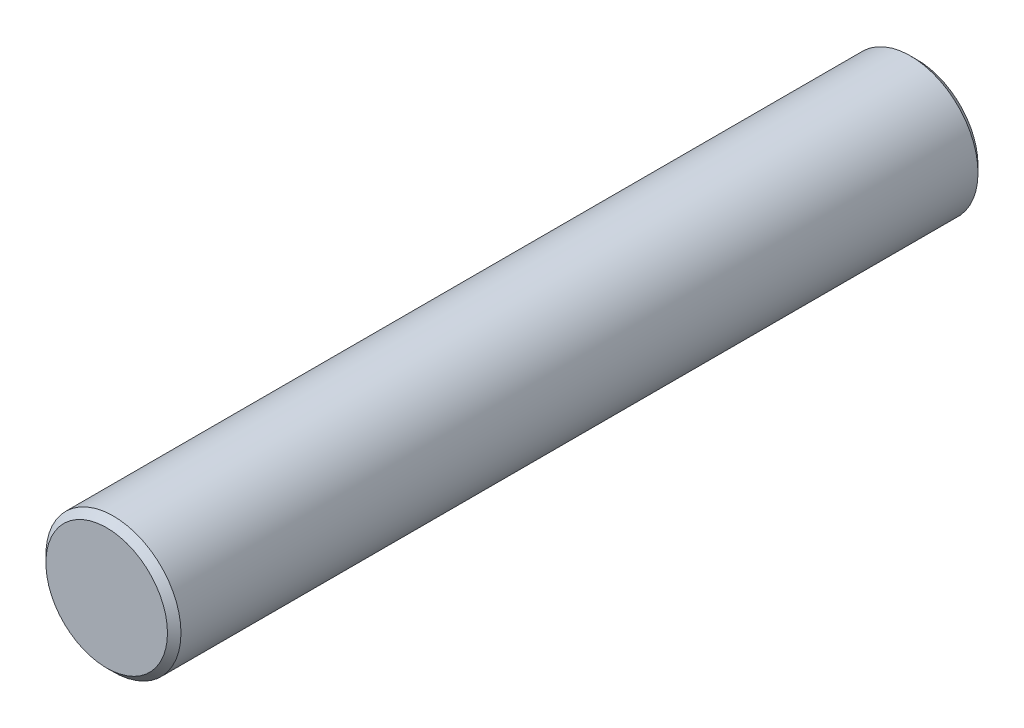
SolidWorks part; units mm, degrees
ref_plane "Plane1" through (0, 0, 0) normal (0, 0, 1) x (1, 0, 0)
ref_plane "Plane2" through (0, 0, 0) normal (0, 1, 0) x (1, 0, 0)
ref_plane "Plane3" through (0, 0, 0) normal (1, 0, 0) x (0, 0, -1)
sketch "Esquisse1" plane through (0, 0, 0) normal (0, 0, 1) x (1, 0, 0)
  circle A0 centre (0, 0) radius 2.5
  dimension "D1" = 5
extrude "Base-Extrusion" add sketch "Esquisse1" along normal blind 30
chamfer "Chanfrein1" distance 0.25 angle 45
